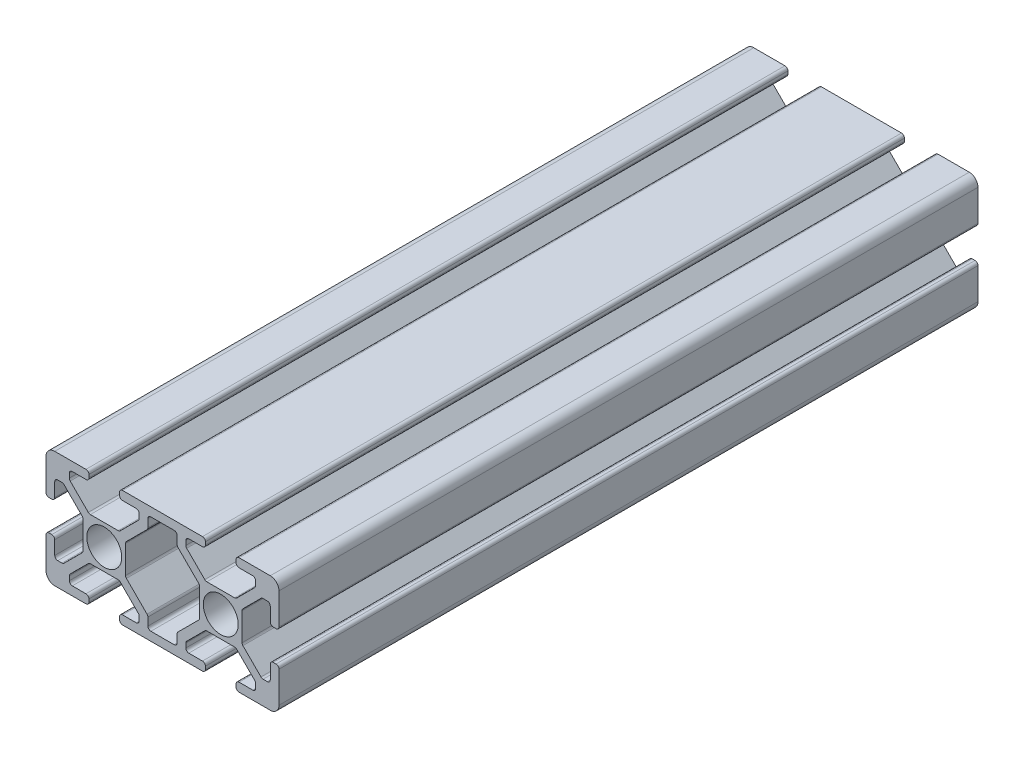
SolidWorks part; units mm, degrees
material "6105-T5 Aluminum"
ref_plane "Front Plane" through (0, 0, 0) normal (0, 0, 1) x (1, 0, 0)
ref_plane "Top Plane" through (0, 0, 0) normal (0, 1, 0) x (1, 0, 0)
ref_plane "Right Plane" through (0, 0, 0) normal (1, 0, 0) x (0, 0, -1)
sketch "Sketch1" plane through (0, 0, 0) normal (0, 0, 1) x (1, 0, 0)
  line L0 (-10, -10) -> (-10, 10) construction
  line L4 (-12.505, -7.992) -> (-12.505, -6.6448)
  line L5 (-12.6538, -6.2856) -> (-16.1962, -2.7431)
  line L6 (-16.345, -2.3839) -> (-16.345, 2.3839)
  line L7 (-16.1962, 2.7431) -> (-12.6538, 6.2856)
  line L8 (-12.505, 6.6448) -> (-12.505, 7.992)
  line L9 (-11.997, 8.5) -> (-8.003, 8.5)
  line L10 (-7.495, 7.992) -> (-7.495, 6.6448)
  line L11 (-7.3462, 6.2856) -> (-3.8038, 2.7431)
  line L12 (-3.655, 2.3839) -> (-3.655, -2.3839)
  line L13 (-3.8038, -2.7431) -> (-7.3462, -6.2856)
  line L14 (-7.495, -6.6448) -> (-7.495, -7.992)
  line L15 (-8.003, -8.5) -> (-11.997, -8.5)
  line L20 (-22.3839, -3.655) -> (-17.6161, -3.655)
  line L21 (-17.2569, -3.8038) -> (-14.1538, -6.9069)
  line L22 (-14.005, -7.2661) -> (-14.005, -7.992)
  line L23 (-14.513, -8.5) -> (-16.862, -8.5)
  line L24 (-17.37, -9.008) -> (-17.37, -9.492)
  line L25 (-16.862, -10) -> (-3.138, -10)
  line L26 (-2.63, -9.492) -> (-2.63, -9.008)
  line L27 (-3.138, -8.5) -> (-5.487, -8.5)
  line L28 (-5.995, -7.992) -> (-5.995, -7.2661)
  line L29 (-5.8462, -6.9069) -> (-2.7431, -3.8038)
  line L30 (-2.3839, -3.655) -> (2.3839, -3.655)
  line L31 (2.7431, -3.8038) -> (5.8462, -6.9069)
  line L32 (5.995, -7.2661) -> (5.995, -7.992)
  line L33 (5.487, -8.5) -> (3.138, -8.5)
  line L34 (2.63, -9.008) -> (2.63, -9.492)
  line L35 (3.138, -10) -> (8.5, -10)
  line L36 (10, -8.5) -> (10, -3.138)
  line L37 (9.492, -2.63) -> (9.008, -2.63)
  line L38 (8.5, -3.138) -> (8.5, -5.487)
  line L39 (7.992, -5.995) -> (7.2661, -5.995)
  line L40 (6.9069, -5.8462) -> (3.8038, -2.7431)
  line L41 (3.655, -2.3839) -> (3.655, 2.3839)
  line L42 (3.8038, 2.7431) -> (6.9069, 5.8462)
  line L43 (7.2661, 5.995) -> (7.992, 5.995)
  line L44 (8.5, 5.487) -> (8.5, 3.138)
  line L45 (9.008, 2.63) -> (9.492, 2.63)
  line L46 (10, 3.138) -> (10, 8.5)
  line L47 (8.5, 10) -> (3.138, 10)
  line L48 (2.63, 9.492) -> (2.63, 9.008)
  line L49 (3.138, 8.5) -> (5.487, 8.5)
  line L50 (5.995, 7.992) -> (5.995, 7.2661)
  line L51 (5.8462, 6.9069) -> (2.7431, 3.8038)
  line L52 (2.3839, 3.655) -> (-2.3839, 3.655)
  line L53 (-2.7431, 3.8038) -> (-5.8462, 6.9069)
  line L54 (-5.995, 7.2661) -> (-5.995, 7.992)
  line L55 (-5.487, 8.5) -> (-3.138, 8.5)
  line L56 (-2.63, 9.008) -> (-2.63, 9.492)
  line L57 (-3.138, 10) -> (-16.862, 10)
  line L58 (-17.37, 9.492) -> (-17.37, 9.008)
  line L59 (-16.862, 8.5) -> (-14.513, 8.5)
  line L60 (-14.005, 7.992) -> (-14.005, 7.2661)
  line L61 (-14.1538, 6.9069) -> (-17.2569, 3.8038)
  line L62 (-17.6161, 3.655) -> (-22.3839, 3.655)
  line L63 (-22.7431, 3.8038) -> (-25.8462, 6.9069)
  line L64 (-25.995, 7.2661) -> (-25.995, 7.992)
  line L65 (-25.487, 8.5) -> (-23.138, 8.5)
  line L66 (-22.63, 9.008) -> (-22.63, 9.492)
  line L67 (-23.138, 10) -> (-28.5, 10)
  line L68 (-30, 8.5) -> (-30, 3.138)
  line L69 (-29.492, 2.63) -> (-29.008, 2.63)
  line L70 (-28.5, 3.138) -> (-28.5, 5.487)
  line L71 (-27.992, 5.995) -> (-27.2661, 5.995)
  line L72 (-26.9069, 5.8462) -> (-23.8038, 2.7431)
  line L73 (-23.655, 2.3839) -> (-23.655, -2.3839)
  line L74 (-23.8038, -2.7431) -> (-26.9069, -5.8462)
  line L75 (-27.2661, -5.995) -> (-27.992, -5.995)
  line L76 (-28.5, -5.487) -> (-28.5, -3.138)
  line L77 (-29.008, -2.63) -> (-29.492, -2.63)
  line L78 (-30, -3.138) -> (-30, -8.5)
  line L79 (-28.5, -10) -> (-23.138, -10)
  line L80 (-22.63, -9.492) -> (-22.63, -9.008)
  line L81 (-23.138, -8.5) -> (-25.487, -8.5)
  line L82 (-25.995, -7.992) -> (-25.995, -7.2661)
  line L83 (-25.8462, -6.9069) -> (-22.7431, -3.8038)
  circle A0 centre (-20, 0) radius 3
  arc A12 (-12.505, -7.992) -> (-11.997, -8.5) centre (-11.997, -7.992) ccw
  arc A13 (-12.505, -6.6448) -> (-12.6538, -6.2856) centre (-13.013, -6.6448) ccw
  arc A14 (-16.345, -2.3839) -> (-16.1962, -2.7431) centre (-15.837, -2.3839) ccw
  arc A15 (-16.1962, 2.7431) -> (-16.345, 2.3839) centre (-15.837, 2.3839) ccw
  arc A16 (-12.6538, 6.2856) -> (-12.505, 6.6448) centre (-13.013, 6.6448) ccw
  arc A17 (-11.997, 8.5) -> (-12.505, 7.992) centre (-11.997, 7.992) ccw
  arc A18 (-7.495, 7.992) -> (-8.003, 8.5) centre (-8.003, 7.992) ccw
  arc A19 (-7.495, 6.6448) -> (-7.3462, 6.2856) centre (-6.987, 6.6448) ccw
  arc A20 (-3.655, 2.3839) -> (-3.8038, 2.7431) centre (-4.163, 2.3839) ccw
  arc A21 (-3.8038, -2.7431) -> (-3.655, -2.3839) centre (-4.163, -2.3839) ccw
  arc A22 (-7.3462, -6.2856) -> (-7.495, -6.6448) centre (-6.987, -6.6448) ccw
  arc A23 (-8.003, -8.5) -> (-7.495, -7.992) centre (-8.003, -7.992) ccw
  arc A36 (-22.3839, -3.655) -> (-22.7431, -3.8038) centre (-22.3839, -4.163) ccw
  arc A37 (-17.2569, -3.8038) -> (-17.6161, -3.655) centre (-17.6161, -4.163) ccw
  arc A38 (-14.005, -7.2661) -> (-14.1538, -6.9069) centre (-14.513, -7.2661) ccw
  arc A39 (-14.513, -8.5) -> (-14.005, -7.992) centre (-14.513, -7.992) ccw
  arc A40 (-16.862, -8.5) -> (-17.37, -9.008) centre (-16.862, -9.008) ccw
  arc A41 (-17.37, -9.492) -> (-16.862, -10) centre (-16.862, -9.492) ccw
  arc A42 (-3.138, -10) -> (-2.63, -9.492) centre (-3.138, -9.492) ccw
  arc A43 (-2.63, -9.008) -> (-3.138, -8.5) centre (-3.138, -9.008) ccw
  arc A44 (-5.995, -7.992) -> (-5.487, -8.5) centre (-5.487, -7.992) ccw
  arc A45 (-5.8462, -6.9069) -> (-5.995, -7.2661) centre (-5.487, -7.2661) ccw
  arc A46 (-2.3839, -3.655) -> (-2.7431, -3.8038) centre (-2.3839, -4.163) ccw
  arc A47 (2.7431, -3.8038) -> (2.3839, -3.655) centre (2.3839, -4.163) ccw
  arc A48 (5.995, -7.2661) -> (5.8462, -6.9069) centre (5.487, -7.2661) ccw
  arc A49 (5.487, -8.5) -> (5.995, -7.992) centre (5.487, -7.992) ccw
  arc A50 (3.138, -8.5) -> (2.63, -9.008) centre (3.138, -9.008) ccw
  arc A51 (2.63, -9.492) -> (3.138, -10) centre (3.138, -9.492) ccw
  arc A52 (8.5, -10) -> (10, -8.5) centre (8.5, -8.5) ccw
  arc A53 (10, -3.138) -> (9.492, -2.63) centre (9.492, -3.138) ccw
  arc A54 (9.008, -2.63) -> (8.5, -3.138) centre (9.008, -3.138) ccw
  arc A55 (7.992, -5.995) -> (8.5, -5.487) centre (7.992, -5.487) ccw
  arc A56 (6.9069, -5.8462) -> (7.2661, -5.995) centre (7.2661, -5.487) ccw
  arc A57 (3.655, -2.3839) -> (3.8038, -2.7431) centre (4.163, -2.3839) ccw
  arc A58 (3.8038, 2.7431) -> (3.655, 2.3839) centre (4.163, 2.3839) ccw
  arc A59 (7.2661, 5.995) -> (6.9069, 5.8462) centre (7.2661, 5.487) ccw
  arc A60 (8.5, 5.487) -> (7.992, 5.995) centre (7.992, 5.487) ccw
  arc A61 (8.5, 3.138) -> (9.008, 2.63) centre (9.008, 3.138) ccw
  arc A62 (9.492, 2.63) -> (10, 3.138) centre (9.492, 3.138) ccw
  arc A63 (10, 8.5) -> (8.5, 10) centre (8.5, 8.5) ccw
  arc A64 (3.138, 10) -> (2.63, 9.492) centre (3.138, 9.492) ccw
  arc A65 (2.63, 9.008) -> (3.138, 8.5) centre (3.138, 9.008) ccw
  arc A66 (5.995, 7.992) -> (5.487, 8.5) centre (5.487, 7.992) ccw
  arc A67 (5.8462, 6.9069) -> (5.995, 7.2661) centre (5.487, 7.2661) ccw
  arc A68 (2.3839, 3.655) -> (2.7431, 3.8038) centre (2.3839, 4.163) ccw
  arc A69 (-2.7431, 3.8038) -> (-2.3839, 3.655) centre (-2.3839, 4.163) ccw
  arc A70 (-5.995, 7.2661) -> (-5.8462, 6.9069) centre (-5.487, 7.2661) ccw
  arc A71 (-5.487, 8.5) -> (-5.995, 7.992) centre (-5.487, 7.992) ccw
  arc A72 (-3.138, 8.5) -> (-2.63, 9.008) centre (-3.138, 9.008) ccw
  arc A73 (-2.63, 9.492) -> (-3.138, 10) centre (-3.138, 9.492) ccw
  arc A74 (-16.862, 10) -> (-17.37, 9.492) centre (-16.862, 9.492) ccw
  arc A75 (-17.37, 9.008) -> (-16.862, 8.5) centre (-16.862, 9.008) ccw
  arc A76 (-14.005, 7.992) -> (-14.513, 8.5) centre (-14.513, 7.992) ccw
  arc A77 (-14.1538, 6.9069) -> (-14.005, 7.2661) centre (-14.513, 7.2661) ccw
  arc A78 (-17.6161, 3.655) -> (-17.2569, 3.8038) centre (-17.6161, 4.163) ccw
  arc A79 (-22.7431, 3.8038) -> (-22.3839, 3.655) centre (-22.3839, 4.163) ccw
  arc A80 (-25.995, 7.2661) -> (-25.8462, 6.9069) centre (-25.487, 7.2661) ccw
  arc A81 (-25.487, 8.5) -> (-25.995, 7.992) centre (-25.487, 7.992) ccw
  arc A82 (-23.138, 8.5) -> (-22.63, 9.008) centre (-23.138, 9.008) ccw
  arc A83 (-22.63, 9.492) -> (-23.138, 10) centre (-23.138, 9.492) ccw
  arc A84 (-28.5, 10) -> (-30, 8.5) centre (-28.5, 8.5) ccw
  arc A85 (-30, 3.138) -> (-29.492, 2.63) centre (-29.492, 3.138) ccw
  arc A86 (-29.008, 2.63) -> (-28.5, 3.138) centre (-29.008, 3.138) ccw
  arc A87 (-27.992, 5.995) -> (-28.5, 5.487) centre (-27.992, 5.487) ccw
  arc A88 (-26.9069, 5.8462) -> (-27.2661, 5.995) centre (-27.2661, 5.487) ccw
  arc A89 (-23.655, 2.3839) -> (-23.8038, 2.7431) centre (-24.163, 2.3839) ccw
  arc A90 (-23.8038, -2.7431) -> (-23.655, -2.3839) centre (-24.163, -2.3839) ccw
  arc A91 (-27.2661, -5.995) -> (-26.9069, -5.8462) centre (-27.2661, -5.487) ccw
  arc A92 (-28.5, -5.487) -> (-27.992, -5.995) centre (-27.992, -5.487) ccw
  arc A93 (-28.5, -3.138) -> (-29.008, -2.63) centre (-29.008, -3.138) ccw
  arc A94 (-29.492, -2.63) -> (-30, -3.138) centre (-29.492, -3.138) ccw
  arc A95 (-30, -8.5) -> (-28.5, -10) centre (-28.5, -8.5) ccw
  arc A96 (-23.138, -10) -> (-22.63, -9.492) centre (-23.138, -9.492) ccw
  arc A97 (-22.63, -9.008) -> (-23.138, -8.5) centre (-23.138, -9.008) ccw
  arc A98 (-25.995, -7.992) -> (-25.487, -8.5) centre (-25.487, -7.992) ccw
  arc A99 (-25.8462, -6.9069) -> (-25.995, -7.2661) centre (-25.487, -7.2661) ccw
  circle A100 centre (0, 0) radius 3
  dimension "D1" = 6
extrude "Extrude1" add sketch "Sketch1" against normal blind 120
